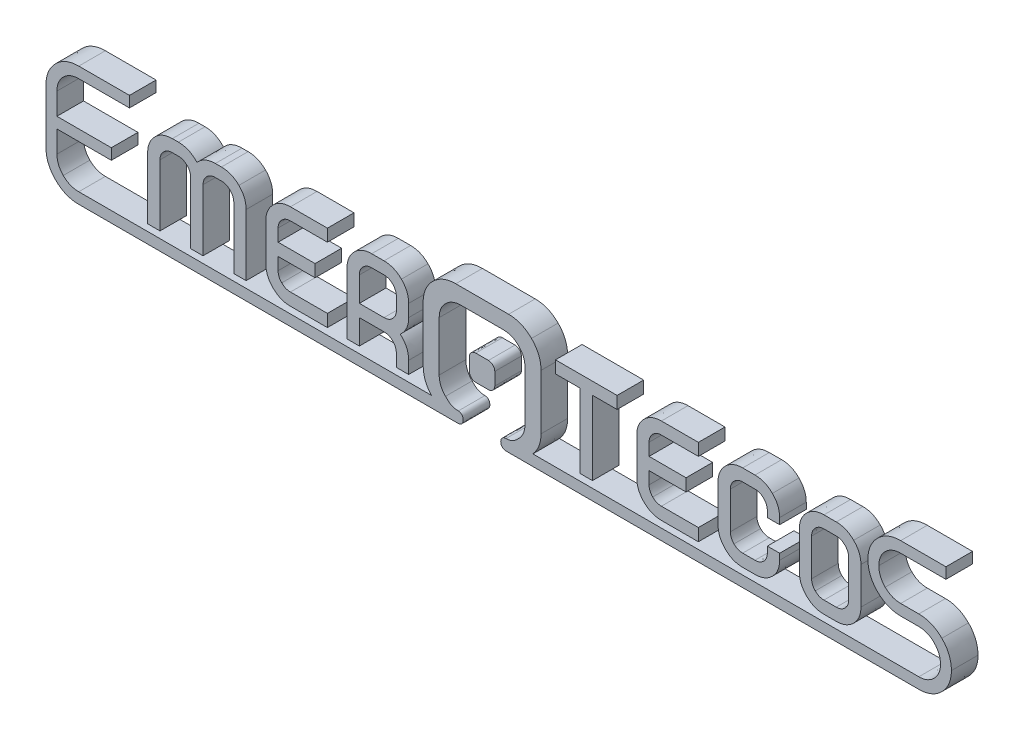
SolidWorks part; units mm, degrees
ref_plane "Plano frontal" through (0, 0, 0) normal (0, 0, 1) x (1, 0, 0)
ref_plane "Plano superior" through (0, 0, 0) normal (0, 1, 0) x (1, 0, 0)
ref_plane "Plano direito" through (0, 0, 0) normal (1, 0, 0) x (0, 0, -1)
sketch "Esboço1" plane through (0, 0, 0) normal (0, 0, 1) x (1, 0, 0)
  line L0 (31.8016, 20.6464) -> (31.8016, -20.6469)
  line L1 (315.8226, -4.1046) -> (302.1879, -4.1046)
  line L2 (302.1879, 45.0088) -> (336.201, 45.0088)
  line L3 (336.201, 45.0088) -> (336.201, 36.7985)
  line L4 (336.201, 36.7985) -> (302.1879, 36.7985)
  line L5 (302.1879, 4.1051) -> (315.8226, 4.1051)
  line L6 (19.7513, -20.6469) -> (19.7513, 16.7655)
  line L7 (3.559, 32.9578) -> (-28.3883, 32.9578)
  line L8 (-44.7261, 16.7655) -> (-44.7261, -20.6469)
  line L9 (-340.3059, -20.525) -> (-340.3059, 20.5247)
  line L10 (-315.6763, 45.008) -> (-277.5585, 45.008)
  line L11 (-277.5585, 45.008) -> (-277.5585, 36.7977)
  line L12 (-277.5585, 36.7977) -> (-315.6763, 36.7977)
  line L13 (-332.0959, 20.5247) -> (-332.0959, 4.1049)
  line L14 (-332.0959, 4.1049) -> (-291.193, 4.1049)
  line L15 (-291.193, 4.1049) -> (-291.193, -4.1051)
  line L16 (-291.193, -4.1051) -> (-332.0959, -4.1051)
  line L17 (-332.0959, -4.1051) -> (-332.0959, -20.525)
  line L18 (-56.7764, -20.6469) -> (-56.7764, 20.6464)
  line L19 (-32.2694, 45.0078) -> (7.4404, 45.0078)
  line L20 (-17.2563, 7.3769) -> (-7.718, 7.3769)
  line L21 (-2.9492, 2.6083) -> (-2.9492, -6.9301)
  line L22 (-7.718, -11.6987) -> (-17.2563, -11.6987)
  line L23 (-22.0248, -6.9301) -> (-22.0248, 2.6083)
  line L24 (253.7724, -31.7851) -> (244.5085, -31.7851)
  line L25 (225.981, -13.2573) -> (225.981, 14.5341)
  line L26 (244.5085, 32.9578) -> (253.7724, 32.9578)
  line L27 (272.3002, 14.5341) -> (272.3002, -13.2573)
  line L28 (263.0363, -13.2573) -> (263.0363, 14.5341)
  line L29 (253.7724, 23.798) -> (244.5085, 23.798)
  line L30 (235.2446, 14.5341) -> (235.2446, -13.2573)
  line L31 (244.5085, -22.5212) -> (253.7724, -22.5212)
  line L32 (-67.6758, -31.7851) -> (-76.9396, -31.7851)
  line L33 (-76.9396, -31.7851) -> (-76.9396, -22.5212)
  line L34 (-86.2035, -13.2573) -> (-104.7313, -13.2573)
  line L35 (-104.7313, -13.2573) -> (-104.7313, -31.7851)
  line L36 (-104.7313, -31.7851) -> (-113.9949, -31.7851)
  line L37 (-113.9949, -31.7851) -> (-113.9949, 14.5341)
  line L38 (-95.4674, 32.9578) -> (-86.2035, 32.9578)
  line L39 (-67.6758, 14.5341) -> (-67.6758, 5.2705)
  line L40 (-67.6758, -22.5212) -> (-67.6758, -31.7851)
  line L41 (-76.9396, 5.2705) -> (-76.9396, 14.5341)
  line L42 (-86.2035, 23.798) -> (-95.4674, 23.798)
  line L43 (-104.7313, 14.5341) -> (-104.7313, -3.9934)
  line L44 (-104.7313, -3.9934) -> (-86.2035, -3.9934)
  line L45 (192.6727, -31.7851) -> (183.4088, -31.7851)
  line L46 (164.8813, -13.2573) -> (164.8813, 14.5341)
  line L47 (183.4088, 32.9578) -> (192.6727, 32.9578)
  line L48 (211.2005, 14.5341) -> (211.2005, 9.8501)
  line L49 (211.2005, 9.8501) -> (201.9369, 9.8501)
  line L50 (201.9369, 9.8501) -> (201.9369, 14.5341)
  line L51 (192.6727, 23.798) -> (183.4088, 23.798)
  line L52 (174.1452, 14.5341) -> (174.1452, -13.2573)
  line L53 (183.4088, -22.5212) -> (192.6727, -22.5212)
  line L54 (201.9369, -13.2573) -> (201.9369, -8.6774)
  line L55 (201.9369, -8.6774) -> (211.2005, -8.6774)
  line L56 (211.2005, -8.6774) -> (211.2005, -13.2573)
  line L57 (150.101, -31.7851) -> (122.3094, -31.7851)
  line L58 (103.7819, -13.2573) -> (103.7819, 14.5341)
  line L59 (122.3094, 32.9578) -> (150.101, 32.9578)
  line L60 (150.101, 32.9578) -> (150.101, 23.798)
  line L61 (150.101, 23.798) -> (122.3094, 23.798)
  line L62 (113.0455, 14.5341) -> (113.0455, 5.2705)
  line L63 (113.0455, 5.2705) -> (140.8372, 5.2705)
  line L64 (140.8372, 5.2705) -> (140.8372, -3.9934)
  line L65 (140.8372, -3.9934) -> (113.0455, -3.9934)
  line L66 (113.0455, -3.9934) -> (113.0455, -13.2573)
  line L67 (122.3094, -22.5212) -> (150.101, -22.5212)
  line L68 (150.101, -22.5212) -> (150.101, -31.7851)
  line L69 (89.0013, 23.798) -> (70.4736, 23.798)
  line L70 (70.4736, 23.798) -> (70.4736, -31.7851)
  line L71 (70.4736, -31.7851) -> (61.2097, -31.7851)
  line L72 (61.2097, -31.7851) -> (61.2097, 23.798)
  line L73 (61.2097, 23.798) -> (42.6822, 23.798)
  line L74 (42.6822, 23.798) -> (42.6822, 32.9578)
  line L75 (42.6822, 32.9578) -> (89.0013, 32.9578)
  line L76 (89.0013, 32.9578) -> (89.0013, 23.798)
  line L77 (-128.7755, -31.7851) -> (-156.5671, -31.7851)
  line L78 (-175.0946, -13.2573) -> (-175.0946, 14.5341)
  line L79 (-156.5671, 32.9578) -> (-128.7755, 32.9578)
  line L80 (-128.7755, 32.9578) -> (-128.7755, 23.798)
  line L81 (-128.7755, 23.798) -> (-156.5671, 23.798)
  line L82 (-165.8308, 14.5341) -> (-165.8308, 5.2705)
  line L83 (-165.8308, 5.2705) -> (-138.0391, 5.2705)
  line L84 (-138.0391, 5.2705) -> (-138.0391, -3.9934)
  line L85 (-138.0391, -3.9934) -> (-165.8308, -3.9934)
  line L86 (-165.8308, -3.9934) -> (-165.8308, -13.2573)
  line L87 (-156.5671, -22.5212) -> (-128.7755, -22.5212)
  line L88 (-128.7755, -22.5212) -> (-128.7755, -31.7851)
  line L89 (-189.8752, -31.7851) -> (-199.139, -31.7851)
  line L90 (-199.139, -31.7851) -> (-199.139, 14.5341)
  line L91 (-208.4029, 23.798) -> (-212.9828, 23.798)
  line L92 (-222.2467, 14.5341) -> (-222.2467, -31.7851)
  line L93 (-222.2467, -31.7851) -> (-231.5103, -31.7851)
  line L94 (-231.5103, -31.7851) -> (-231.5103, 14.5341)
  line L95 (-240.7742, 23.798) -> (-245.3541, 23.798)
  line L96 (-254.618, 14.5341) -> (-254.618, -31.7851)
  line L97 (-254.618, -31.7851) -> (-263.8816, -31.7851)
  line L98 (-263.8816, -31.7851) -> (-263.8816, 14.5341)
  line L99 (-245.3541, 32.9578) -> (-240.7742, 32.9578)
  line L100 (-212.9828, 32.9578) -> (-208.4029, 32.9578)
  line L101 (-189.8752, 14.5341) -> (-189.8752, -31.7851)
  spline S0 degree 3 poles (7.4404, 45.0078) (14.1506, 45.0078) (19.8885, 42.625) (24.6537, 37.8597) knots 0 0 0 0 0.015385 0.015385 0.015385 0.015385
  spline S1 degree 3 poles (24.6537, 37.8597) (29.419, 33.0944) (31.8016, 27.3543) (31.8016, 20.6464) knots 0.015385 0.015385 0.015385 0.015385 0.030769 0.030769 0.030769 0.030769
  spline S2 degree 3 poles (31.8016, -20.6469) (31.8016, -26.8638) (29.7551, -32.2496) (25.6619, -36.7982) knots 0.046154 0.046154 0.046154 0.046154 0.061538 0.061538 0.061538 0.061538
  spline S3 degree 3 poles (25.6619, -36.7982) (122.382, -36.7982) (219.1024, -36.7982) (315.8226, -36.7982) knots 0.061538 0.061538 0.061538 0.061538 0.076923 0.076923 0.076923 0.076923
  spline S4 degree 3 poles (315.8226, -36.7982) (320.3184, -36.7982) (324.1545, -35.21) (327.3311, -32.0337) knots 0.076923 0.076923 0.076923 0.076923 0.092308 0.092308 0.092308 0.092308
  spline S5 degree 3 poles (327.3311, -32.0337) (330.5076, -28.8569) (332.0959, -25.0208) (332.0959, -20.525) knots 0.092308 0.092308 0.092308 0.092308 0.107692 0.107692 0.107692 0.107692
  spline S6 degree 3 poles (332.0959, -20.525) (332.0959, -15.9311) (330.5076, -12.0459) (327.3311, -8.8694) knots 0.107692 0.107692 0.107692 0.107692 0.123077 0.123077 0.123077 0.123077
  spline S7 degree 3 poles (327.3311, -8.8694) (324.1545, -5.6929) (320.3184, -4.1046) (315.8226, -4.1046) knots 0.123077 0.123077 0.123077 0.123077 0.138462 0.138462 0.138462 0.138462
  spline S8 degree 3 poles (302.1879, -4.1046) (295.3464, -4.1046) (289.531, -1.7102) (284.7416, 3.0787) knots 0.153846 0.153846 0.153846 0.153846 0.169231 0.169231 0.169231 0.169231
  spline S9 degree 3 poles (284.7416, 3.0787) (279.9524, 7.8682) (277.5582, 13.6835) (277.5582, 20.5252) knots 0.169231 0.169231 0.169231 0.169231 0.184615 0.184615 0.184615 0.184615
  spline S10 degree 3 poles (277.5582, 20.5252) (277.5582, 27.2692) (279.9524, 33.0357) (284.7416, 37.8249) knots 0.184615 0.184615 0.184615 0.184615 0.2 0.2 0.2 0.2
  spline S11 degree 3 poles (284.7416, 37.8249) (289.531, 42.6141) (295.3464, 45.0088) (302.1879, 45.0088) knots 0.2 0.2 0.2 0.2 0.215385 0.215385 0.215385 0.215385
  spline S12 degree 3 poles (302.1879, 36.7985) (297.5943, 36.7985) (293.7093, 35.2102) (290.5328, 32.0337) knots 0.261538 0.261538 0.261538 0.261538 0.276923 0.276923 0.276923 0.276923
  spline S13 degree 3 poles (290.5328, 32.0337) (287.3563, 28.8574) (285.768, 25.021) (285.768, 20.5252) knots 0.276923 0.276923 0.276923 0.276923 0.292308 0.292308 0.292308 0.292308
  spline S14 degree 3 poles (285.768, 20.5252) (285.768, 15.9314) (287.3563, 12.0465) (290.5328, 8.8699) knots 0.292308 0.292308 0.292308 0.292308 0.307692 0.307692 0.307692 0.307692
  spline S15 degree 3 poles (290.5328, 8.8699) (293.7093, 5.6934) (297.5943, 4.1051) (302.1879, 4.1051) knots 0.307692 0.307692 0.307692 0.307692 0.323077 0.323077 0.323077 0.323077
  spline S16 degree 3 poles (315.8226, 4.1051) (322.5663, 4.1051) (328.3331, 1.7104) (333.1223, -3.0787) knots 0.338462 0.338462 0.338462 0.338462 0.353846 0.353846 0.353846 0.353846
  spline S17 degree 3 poles (333.1223, -3.0787) (337.9114, -7.8677) (340.3062, -13.6832) (340.3062, -20.525) knots 0.353846 0.353846 0.353846 0.353846 0.369231 0.369231 0.369231 0.369231
  spline S18 degree 3 poles (340.3062, -20.525) (340.3062, -27.2687) (337.9114, -33.0352) (333.1223, -37.8244) knots 0.369231 0.369231 0.369231 0.369231 0.384615 0.384615 0.384615 0.384615
  spline S19 degree 3 poles (333.1223, -37.8244) (328.3331, -42.6136) (322.5663, -45.0083) (315.8226, -45.0083) knots 0.384615 0.384615 0.384615 0.384615 0.4 0.4 0.4 0.4
  spline S20 degree 3 poles (315.8226, -45.0083) (212.439, -45.0075) (109.0554, -45.008) (5.6718, -45.008) knots 0.4 0.4 0.4 0.4 0.415385 0.415385 0.415385 0.415385
  spline S21 degree 3 poles (5.6718, -45.008) (0.098, -45.0197) (0.2543, -36.8391) (5.5517, -36.8391) knots 0.415385 0.415385 0.415385 0.415385 0.430769 0.430769 0.430769 0.430769
  spline S22 degree 3 poles (5.5517, -36.8391) (10.2634, -36.6761) (11.7356, -35.3728) (15.0104, -32.0982) knots 0.430769 0.430769 0.430769 0.430769 0.446154 0.446154 0.446154 0.446154
  spline S23 degree 3 poles (15.0104, -32.0982) (18.1709, -28.9375) (19.7513, -25.1206) (19.7513, -20.6469) knots 0.446154 0.446154 0.446154 0.446154 0.461538 0.461538 0.461538 0.461538
  spline S24 degree 3 poles (19.7513, 16.7655) (19.7513, 21.239) (18.1709, 25.0563) (15.0104, 28.2169) knots 0.476923 0.476923 0.476923 0.476923 0.492308 0.492308 0.492308 0.492308
  spline S25 degree 3 poles (15.0104, 28.2169) (11.8496, 31.3774) (8.03, 32.9578) (3.559, 32.9578) knots 0.492308 0.492308 0.492308 0.492308 0.507692 0.507692 0.507692 0.507692
  spline S26 degree 3 poles (-28.3883, 32.9578) (-32.9565, 32.9578) (-36.8247, 31.3774) (-39.9854, 28.2169) knots 0.523077 0.523077 0.523077 0.523077 0.538462 0.538462 0.538462 0.538462
  spline S27 degree 3 poles (-39.9854, 28.2169) (-43.146, 25.0563) (-44.7261, 21.238) (-44.7261, 16.7655) knots 0.538462 0.538462 0.538462 0.538462 0.553846 0.553846 0.553846 0.553846
  spline S28 degree 3 poles (-44.7261, -20.6469) (-44.7261, -25.1196) (-43.146, -28.9375) (-39.9854, -32.0982) knots 0.569231 0.569231 0.569231 0.569231 0.584615 0.584615 0.584615 0.584615
  spline S29 degree 3 poles (-39.9854, -32.0982) (-36.6634, -35.4198) (-35.1465, -36.6781) (-30.3809, -36.8391) knots 0.584615 0.584615 0.584615 0.584615 0.6 0.6 0.6 0.6
  spline S30 degree 3 poles (-30.3809, -36.8391) (-25.4048, -36.8391) (-25.4048, -45.0083) (-30.3809, -45.0083) knots 0.6 0.6 0.6 0.6 0.615385 0.615385 0.615385 0.615385
  spline S31 degree 3 poles (-30.3809, -45.0083) (-125.4793, -45.0083) (-220.5779, -45.0083) (-315.6763, -45.0083) knots 0.615385 0.615385 0.615385 0.615385 0.630769 0.630769 0.630769 0.630769
  spline S32 degree 3 poles (-315.6763, -45.0083) (-322.5178, -45.0083) (-328.3334, -42.6136) (-333.1223, -37.8244) knots 0.630769 0.630769 0.630769 0.630769 0.646154 0.646154 0.646154 0.646154
  spline S33 degree 3 poles (-333.1223, -37.8244) (-337.9114, -33.0355) (-340.3059, -27.2687) (-340.3059, -20.525) knots 0.646154 0.646154 0.646154 0.646154 0.661538 0.661538 0.661538 0.661538
  spline S34 degree 3 poles (-340.3059, 20.5247) (-340.3059, 27.2684) (-337.9114, 33.0352) (-333.1223, 37.8242) knots 0.676923 0.676923 0.676923 0.676923 0.692308 0.692308 0.692308 0.692308
  spline S35 degree 3 poles (-333.1223, 37.8242) (-328.3334, 42.6133) (-322.5178, 45.008) (-315.6763, 45.008) knots 0.692308 0.692308 0.692308 0.692308 0.707692 0.707692 0.707692 0.707692
  spline S36 degree 3 poles (-315.6763, 36.7977) (-320.2699, 36.7977) (-324.1548, 35.2097) (-327.3313, 32.0332) knots 0.753846 0.753846 0.753846 0.753846 0.769231 0.769231 0.769231 0.769231
  spline S37 degree 3 poles (-327.3313, 32.0332) (-330.5078, 28.8567) (-332.0959, 25.0205) (-332.0959, 20.5247) knots 0.769231 0.769231 0.769231 0.769231 0.784615 0.784615 0.784615 0.784615
  spline S38 degree 3 poles (-332.0959, -20.525) (-332.0959, -25.021) (-330.5078, -28.8569) (-327.3313, -32.0337) knots 0.861538 0.861538 0.861538 0.861538 0.876923 0.876923 0.876923 0.876923
  spline S39 degree 3 poles (-327.3313, -32.0337) (-324.1548, -35.2102) (-320.2699, -36.7985) (-315.6763, -36.7985) knots 0.876923 0.876923 0.876923 0.876923 0.892308 0.892308 0.892308 0.892308
  spline S40 degree 3 poles (-315.6763, -36.7985) (-227.3297, -36.7985) (-138.983, -36.7985) (-50.6364, -36.7985) knots 0.892308 0.892308 0.892308 0.892308 0.907692 0.907692 0.907692 0.907692
  spline S41 degree 3 poles (-50.6364, -36.7985) (-54.7299, -32.2501) (-56.7764, -26.8663) (-56.7764, -20.6469) knots 0.907692 0.907692 0.907692 0.907692 0.923077 0.923077 0.923077 0.923077
  spline S42 degree 3 poles (-56.7764, 20.6464) (-56.7764, 27.3566) (-54.3938, 33.0944) (-49.6286, 37.8597) knots 0.938462 0.938462 0.938462 0.938462 0.953846 0.953846 0.953846 0.953846
  spline S43 degree 3 poles (-49.6286, 37.8597) (-44.8633, 42.625) (-39.0769, 45.0078) (-32.2694, 45.0078) knots 0.953846 0.953846 0.953846 0.953846 0.969231 0.969231 0.969231 0.969231
  spline S44 degree 3 poles (-7.718, 7.3769) (-5.095, 7.3769) (-2.9492, 5.2311) (-2.9492, 2.6083) knots 0.111111 0.111111 0.111111 0.111111 0.222222 0.222222 0.222222 0.222222
  spline S45 degree 3 poles (-2.9492, -6.9301) (-2.9492, -9.5529) (-5.095, -11.6987) (-7.718, -11.6987) knots 0.333333 0.333333 0.333333 0.333333 0.444444 0.444444 0.444444 0.444444
  spline S46 degree 3 poles (-17.2563, -11.6987) (-19.8791, -11.6987) (-22.0248, -9.5529) (-22.0248, -6.9301) knots 0.555556 0.555556 0.555556 0.555556 0.666667 0.666667 0.666667 0.666667
  spline S47 degree 3 poles (-22.0248, 2.6083) (-22.0248, 5.2311) (-19.8791, 7.3769) (-17.2563, 7.3769) knots 0.777778 0.777778 0.777778 0.777778 1 1 1 1
  spline S48 degree 3 poles (272.3002, -13.2573) (272.3002, -18.3924) (270.4785, -22.764) (266.8354, -26.3723) knots 0 0 0 0 0.076923 0.076923 0.076923 0.076923
  spline S49 degree 3 poles (266.8354, -26.3723) (263.1923, -29.9806) (258.8379, -31.7851) (253.7724, -31.7851) knots 0.076923 0.076923 0.076923 0.076923 0.153846 0.153846 0.153846 0.153846
  spline S50 degree 3 poles (244.5085, -31.7851) (239.3737, -31.7851) (235.0018, -29.9806) (231.3935, -26.3723) knots 0.230769 0.230769 0.230769 0.230769 0.307692 0.307692 0.307692 0.307692
  spline S51 degree 3 poles (231.3935, -26.3723) (227.7852, -22.764) (225.981, -18.3924) (225.981, -13.2573) knots 0.307692 0.307692 0.307692 0.307692 0.384615 0.384615 0.384615 0.384615
  spline S52 degree 3 poles (225.981, 14.5341) (225.981, 19.5999) (227.7852, 23.9367) (231.3935, 27.5453) knots 0.461538 0.461538 0.461538 0.461538 0.538462 0.538462 0.538462 0.538462
  spline S53 degree 3 poles (231.3935, 27.5453) (235.0018, 31.1536) (239.3737, 32.9578) (244.5085, 32.9578) knots 0.538462 0.538462 0.538462 0.538462 0.615385 0.615385 0.615385 0.615385
  spline S54 degree 3 poles (253.7724, 32.9578) (258.8379, 32.9578) (263.1923, 31.1536) (266.8354, 27.5453) knots 0.692308 0.692308 0.692308 0.692308 0.769231 0.769231 0.769231 0.769231
  spline S55 degree 3 poles (266.8354, 27.5453) (270.4785, 23.9367) (272.3002, 19.5999) (272.3002, 14.5341) knots 0.769231 0.769231 0.769231 0.769231 0.846154 0.846154 0.846154 0.846154
  spline S56 degree 3 poles (263.0363, 14.5341) (263.0363, 17.0322) (262.1341, 19.2009) (260.3299, 21.0398) knots 0.076923 0.076923 0.076923 0.076923 0.153846 0.153846 0.153846 0.153846
  spline S57 degree 3 poles (260.3299, 21.0398) (258.5258, 22.8785) (256.3398, 23.798) (253.7724, 23.798) knots 0.153846 0.153846 0.153846 0.153846 0.230769 0.230769 0.230769 0.230769
  spline S58 degree 3 poles (244.5085, 23.798) (241.9411, 23.798) (239.7552, 22.8785) (237.951, 21.0398) knots 0.307692 0.307692 0.307692 0.307692 0.384615 0.384615 0.384615 0.384615
  spline S59 degree 3 poles (237.951, 21.0398) (236.1466, 19.2009) (235.2446, 17.0322) (235.2446, 14.5341) knots 0.384615 0.384615 0.384615 0.384615 0.461538 0.461538 0.461538 0.461538
  spline S60 degree 3 poles (235.2446, -13.2573) (235.2446, -15.825) (236.1466, -18.0106) (237.951, -19.815) knots 0.538462 0.538462 0.538462 0.538462 0.615385 0.615385 0.615385 0.615385
  spline S61 degree 3 poles (237.951, -19.815) (239.7552, -21.619) (241.9411, -22.5212) (244.5085, -22.5212) knots 0.615385 0.615385 0.615385 0.615385 0.692308 0.692308 0.692308 0.692308
  spline S62 degree 3 poles (253.7724, -22.5212) (256.3398, -22.5212) (258.5258, -21.619) (260.3299, -19.815) knots 0.769231 0.769231 0.769231 0.769231 0.846154 0.846154 0.846154 0.846154
  spline S63 degree 3 poles (260.3299, -19.815) (262.1341, -18.0106) (263.0363, -15.825) (263.0363, -13.2573) knots 0.846154 0.846154 0.846154 0.846154 1 1 1 1
  spline S64 degree 3 poles (-76.9396, -22.5212) (-76.9396, -19.9537) (-77.8419, -17.7678) (-79.646, -15.9636) knots 0.111111 0.111111 0.111111 0.111111 0.166667 0.166667 0.166667 0.166667
  spline S65 degree 3 poles (-79.646, -15.9636) (-81.4504, -14.1595) (-83.6361, -13.2573) (-86.2035, -13.2573) knots 0.166667 0.166667 0.166667 0.166667 0.222222 0.222222 0.222222 0.222222
  spline S66 degree 3 poles (-113.9949, 14.5341) (-113.9949, 19.5999) (-112.1908, 23.9367) (-108.5825, 27.5453) knots 0.444444 0.444444 0.444444 0.444444 0.5 0.5 0.5 0.5
  spline S67 degree 3 poles (-108.5825, 27.5453) (-104.9741, 31.1536) (-100.6023, 32.9578) (-95.4674, 32.9578) knots 0.5 0.5 0.5 0.5 0.555556 0.555556 0.555556 0.555556
  spline S68 degree 3 poles (-86.2035, 32.9578) (-81.138, 32.9578) (-76.7837, 31.1536) (-73.1406, 27.5453) knots 0.611111 0.611111 0.611111 0.611111 0.666667 0.666667 0.666667 0.666667
  spline S69 degree 3 poles (-73.1406, 27.5453) (-69.4974, 23.9367) (-67.6758, 19.5999) (-67.6758, 14.5341) knots 0.666667 0.666667 0.666667 0.666667 0.722222 0.722222 0.722222 0.722222
  spline S70 degree 3 poles (-67.6758, 5.2705) (-67.6758, -0.3503) (-69.7923, -4.9997) (-74.0255, -8.6774) knots 0.777778 0.777778 0.777778 0.777778 0.833333 0.833333 0.833333 0.833333
  spline S71 degree 3 poles (-74.0255, -8.6774) (-69.7923, -12.3551) (-67.6758, -16.9697) (-67.6758, -22.5212) knots 0.833333 0.833333 0.833333 0.833333 0.888889 0.888889 0.888889 0.888889
  spline S72 degree 3 poles (-76.9396, 14.5341) (-76.9396, 17.0322) (-77.8419, 19.2009) (-79.646, 21.0398) knots 0.090909 0.090909 0.090909 0.090909 0.181818 0.181818 0.181818 0.181818
  spline S73 degree 3 poles (-79.646, 21.0398) (-81.4504, 22.8785) (-83.6361, 23.798) (-86.2035, 23.798) knots 0.181818 0.181818 0.181818 0.181818 0.272727 0.272727 0.272727 0.272727
  spline S74 degree 3 poles (-95.4674, 23.798) (-98.0349, 23.798) (-100.2208, 22.8785) (-102.0249, 21.0398) knots 0.363636 0.363636 0.363636 0.363636 0.454545 0.454545 0.454545 0.454545
  spline S75 degree 3 poles (-102.0249, 21.0398) (-103.8294, 19.2009) (-104.7313, 17.0322) (-104.7313, 14.5341) knots 0.454545 0.454545 0.454545 0.454545 0.545455 0.545455 0.545455 0.545455
  spline S76 degree 3 poles (-86.2035, -3.9934) (-83.6361, -3.9934) (-81.4504, -3.0914) (-79.646, -1.287) knots 0.727273 0.727273 0.727273 0.727273 0.818182 0.818182 0.818182 0.818182
  spline S77 degree 3 poles (-79.646, -1.287) (-77.8419, 0.5171) (-76.9396, 2.7031) (-76.9396, 5.2705) knots 0.818182 0.818182 0.818182 0.818182 1 1 1 1
  spline S78 degree 3 poles (211.2005, -13.2573) (211.2005, -18.3924) (209.3788, -22.764) (205.7357, -26.3723) knots 0 0 0 0 0.034483 0.034483 0.034483 0.034483
  spline S79 degree 3 poles (205.7357, -26.3723) (202.0928, -29.9806) (197.7385, -31.7851) (192.6727, -31.7851) knots 0.034483 0.034483 0.034483 0.034483 0.068966 0.068966 0.068966 0.068966
  spline S80 degree 3 poles (183.4088, -31.7851) (178.274, -31.7851) (173.9024, -29.9806) (170.2938, -26.3723) knots 0.103448 0.103448 0.103448 0.103448 0.137931 0.137931 0.137931 0.137931
  spline S81 degree 3 poles (170.2938, -26.3723) (166.6855, -22.764) (164.8813, -18.3924) (164.8813, -13.2573) knots 0.137931 0.137931 0.137931 0.137931 0.172414 0.172414 0.172414 0.172414
  spline S82 degree 3 poles (164.8813, 14.5341) (164.8813, 19.5999) (166.6855, 23.9367) (170.2938, 27.5453) knots 0.206897 0.206897 0.206897 0.206897 0.241379 0.241379 0.241379 0.241379
  spline S83 degree 3 poles (170.2938, 27.5453) (173.9024, 31.1536) (178.274, 32.9578) (183.4088, 32.9578) knots 0.241379 0.241379 0.241379 0.241379 0.275862 0.275862 0.275862 0.275862
  spline S84 degree 3 poles (192.6727, 32.9578) (197.7385, 32.9578) (202.0928, 31.1536) (205.7357, 27.5453) knots 0.310345 0.310345 0.310345 0.310345 0.344828 0.344828 0.344828 0.344828
  spline S85 degree 3 poles (205.7357, 27.5453) (209.3788, 23.9367) (211.2005, 19.5999) (211.2005, 14.5341) knots 0.344828 0.344828 0.344828 0.344828 0.37931 0.37931 0.37931 0.37931
  spline S86 degree 3 poles (201.9369, 14.5341) (201.9369, 17.0322) (201.0344, 19.2009) (199.2302, 21.0398) knots 0.482759 0.482759 0.482759 0.482759 0.517241 0.517241 0.517241 0.517241
  spline S87 degree 3 poles (199.2302, 21.0398) (197.4261, 22.8785) (195.2401, 23.798) (192.6727, 23.798) knots 0.517241 0.517241 0.517241 0.517241 0.551724 0.551724 0.551724 0.551724
  spline S88 degree 3 poles (183.4088, 23.798) (180.8414, 23.798) (178.6555, 22.8785) (176.8513, 21.0398) knots 0.586207 0.586207 0.586207 0.586207 0.62069 0.62069 0.62069 0.62069
  spline S89 degree 3 poles (176.8513, 21.0398) (175.0471, 19.2009) (174.1452, 17.0322) (174.1452, 14.5341) knots 0.62069 0.62069 0.62069 0.62069 0.655172 0.655172 0.655172 0.655172
  spline S90 degree 3 poles (174.1452, -13.2573) (174.1452, -15.825) (175.0471, -18.0106) (176.8513, -19.815) knots 0.689655 0.689655 0.689655 0.689655 0.724138 0.724138 0.724138 0.724138
  spline S91 degree 3 poles (176.8513, -19.815) (178.6555, -21.619) (180.8414, -22.5212) (183.4088, -22.5212) knots 0.724138 0.724138 0.724138 0.724138 0.758621 0.758621 0.758621 0.758621
  spline S92 degree 3 poles (192.6727, -22.5212) (195.2401, -22.5212) (197.4261, -21.619) (199.2302, -19.815) knots 0.793103 0.793103 0.793103 0.793103 0.827586 0.827586 0.827586 0.827586
  spline S93 degree 3 poles (199.2302, -19.815) (201.0344, -18.0106) (201.9369, -15.825) (201.9369, -13.2573) knots 0.827586 0.827586 0.827586 0.827586 0.862069 0.862069 0.862069 0.862069
  spline S94 degree 3 poles (122.3094, -31.7851) (117.1743, -31.7851) (112.8027, -29.9806) (109.1941, -26.3723) knots 0.047619 0.047619 0.047619 0.047619 0.095238 0.095238 0.095238 0.095238
  spline S95 degree 3 poles (109.1941, -26.3723) (105.586, -22.764) (103.7819, -18.3924) (103.7819, -13.2573) knots 0.095238 0.095238 0.095238 0.095238 0.142857 0.142857 0.142857 0.142857
  spline S96 degree 3 poles (103.7819, 14.5341) (103.7819, 19.5999) (105.586, 23.9367) (109.1941, 27.5453) knots 0.190476 0.190476 0.190476 0.190476 0.238095 0.238095 0.238095 0.238095
  spline S97 degree 3 poles (109.1941, 27.5453) (112.8027, 31.1536) (117.1743, 32.9578) (122.3094, 32.9578) knots 0.238095 0.238095 0.238095 0.238095 0.285714 0.285714 0.285714 0.285714
  spline S98 degree 3 poles (122.3094, 23.798) (119.7419, 23.798) (117.556, 22.8785) (115.7519, 21.0398) knots 0.428571 0.428571 0.428571 0.428571 0.47619 0.47619 0.47619 0.47619
  spline S99 degree 3 poles (115.7519, 21.0398) (113.9474, 19.2009) (113.0455, 17.0322) (113.0455, 14.5341) knots 0.47619 0.47619 0.47619 0.47619 0.52381 0.52381 0.52381 0.52381
  spline S100 degree 3 poles (113.0455, -13.2573) (113.0455, -15.825) (113.9474, -18.0106) (115.7519, -19.815) knots 0.761905 0.761905 0.761905 0.761905 0.809524 0.809524 0.809524 0.809524
  spline S101 degree 3 poles (115.7519, -19.815) (117.556, -21.619) (119.7419, -22.5212) (122.3094, -22.5212) knots 0.809524 0.809524 0.809524 0.809524 0.857143 0.857143 0.857143 0.857143
  spline S102 degree 3 poles (-156.5671, -31.7851) (-161.702, -31.7851) (-166.0738, -29.9806) (-169.6822, -26.3723) knots 0.047619 0.047619 0.047619 0.047619 0.095238 0.095238 0.095238 0.095238
  spline S103 degree 3 poles (-169.6822, -26.3723) (-173.2905, -22.764) (-175.0946, -18.3924) (-175.0946, -13.2573) knots 0.095238 0.095238 0.095238 0.095238 0.142857 0.142857 0.142857 0.142857
  spline S104 degree 3 poles (-175.0946, 14.5341) (-175.0946, 19.5999) (-173.2905, 23.9367) (-169.6822, 27.5453) knots 0.190476 0.190476 0.190476 0.190476 0.238095 0.238095 0.238095 0.238095
  spline S105 degree 3 poles (-169.6822, 27.5453) (-166.0738, 31.1536) (-161.702, 32.9578) (-156.5671, 32.9578) knots 0.238095 0.238095 0.238095 0.238095 0.285714 0.285714 0.285714 0.285714
  spline S106 degree 3 poles (-156.5671, 23.798) (-159.1346, 23.798) (-161.3205, 22.8785) (-163.1246, 21.0398) knots 0.428571 0.428571 0.428571 0.428571 0.47619 0.47619 0.47619 0.47619
  spline S107 degree 3 poles (-163.1246, 21.0398) (-164.9288, 19.2009) (-165.8308, 17.0322) (-165.8308, 14.5341) knots 0.47619 0.47619 0.47619 0.47619 0.52381 0.52381 0.52381 0.52381
  spline S108 degree 3 poles (-165.8308, -13.2573) (-165.8308, -15.825) (-164.9288, -18.0106) (-163.1246, -19.815) knots 0.761905 0.761905 0.761905 0.761905 0.809524 0.809524 0.809524 0.809524
  spline S109 degree 3 poles (-163.1246, -19.815) (-161.3205, -21.619) (-159.1346, -22.5212) (-156.5671, -22.5212) knots 0.809524 0.809524 0.809524 0.809524 0.857143 0.857143 0.857143 0.857143
  spline S110 degree 3 poles (-199.139, 14.5341) (-199.139, 17.0322) (-200.041, 19.2009) (-201.8452, 21.0398) knots 0.071429 0.071429 0.071429 0.071429 0.107143 0.107143 0.107143 0.107143
  spline S111 degree 3 poles (-201.8452, 21.0398) (-203.6496, 22.8785) (-205.8353, 23.798) (-208.4029, 23.798) knots 0.107143 0.107143 0.107143 0.107143 0.142857 0.142857 0.142857 0.142857
  spline S112 degree 3 poles (-212.9828, 23.798) (-215.5502, 23.798) (-217.7362, 22.8785) (-219.5403, 21.0398) knots 0.178571 0.178571 0.178571 0.178571 0.214286 0.214286 0.214286 0.214286
  spline S113 degree 3 poles (-219.5403, 21.0398) (-221.3442, 19.2009) (-222.2467, 17.0322) (-222.2467, 14.5341) knots 0.214286 0.214286 0.214286 0.214286 0.25 0.25 0.25 0.25
  spline S114 degree 3 poles (-231.5103, 14.5341) (-231.5103, 17.0322) (-232.4123, 19.2009) (-234.2167, 21.0398) knots 0.357143 0.357143 0.357143 0.357143 0.392857 0.392857 0.392857 0.392857
  spline S115 degree 3 poles (-234.2167, 21.0398) (-236.0209, 22.8785) (-238.2068, 23.798) (-240.7742, 23.798) knots 0.392857 0.392857 0.392857 0.392857 0.428571 0.428571 0.428571 0.428571
  spline S116 degree 3 poles (-245.3541, 23.798) (-247.9215, 23.798) (-250.1075, 22.8785) (-251.9116, 21.0398) knots 0.464286 0.464286 0.464286 0.464286 0.5 0.5 0.5 0.5
  spline S117 degree 3 poles (-251.9116, 21.0398) (-253.716, 19.2009) (-254.618, 17.0322) (-254.618, 14.5341) knots 0.5 0.5 0.5 0.5 0.535714 0.535714 0.535714 0.535714
  spline S118 degree 3 poles (-263.8816, 14.5341) (-263.8816, 19.5999) (-262.0775, 23.9367) (-258.4694, 27.5453) knots 0.642857 0.642857 0.642857 0.642857 0.678571 0.678571 0.678571 0.678571
  spline S119 degree 3 poles (-258.4694, 27.5453) (-254.8608, 31.1536) (-250.4892, 32.9578) (-245.3541, 32.9578) knots 0.678571 0.678571 0.678571 0.678571 0.714286 0.714286 0.714286 0.714286
  spline S120 degree 3 poles (-240.7742, 32.9578) (-235.2231, 32.9578) (-230.5736, 30.876) (-226.8263, 26.7124) knots 0.75 0.75 0.75 0.75 0.785714 0.785714 0.785714 0.785714
  spline S121 degree 3 poles (-226.8263, 26.7124) (-223.1487, 30.876) (-218.534, 32.9578) (-212.9828, 32.9578) knots 0.785714 0.785714 0.785714 0.785714 0.821429 0.821429 0.821429 0.821429
  spline S122 degree 3 poles (-208.4029, 32.9578) (-203.2678, 32.9578) (-198.8962, 31.1536) (-195.2876, 27.5453) knots 0.857143 0.857143 0.857143 0.857143 0.892857 0.892857 0.892857 0.892857
  spline S123 degree 3 poles (-195.2876, 27.5453) (-191.6793, 23.9367) (-189.8752, 19.5999) (-189.8752, 14.5341) knots 0.892857 0.892857 0.892857 0.892857 0.928571 0.928571 0.928571 0.928571
extrude "Ressalto-extrusão1" add sketch "Esboço1" along normal blind 20
